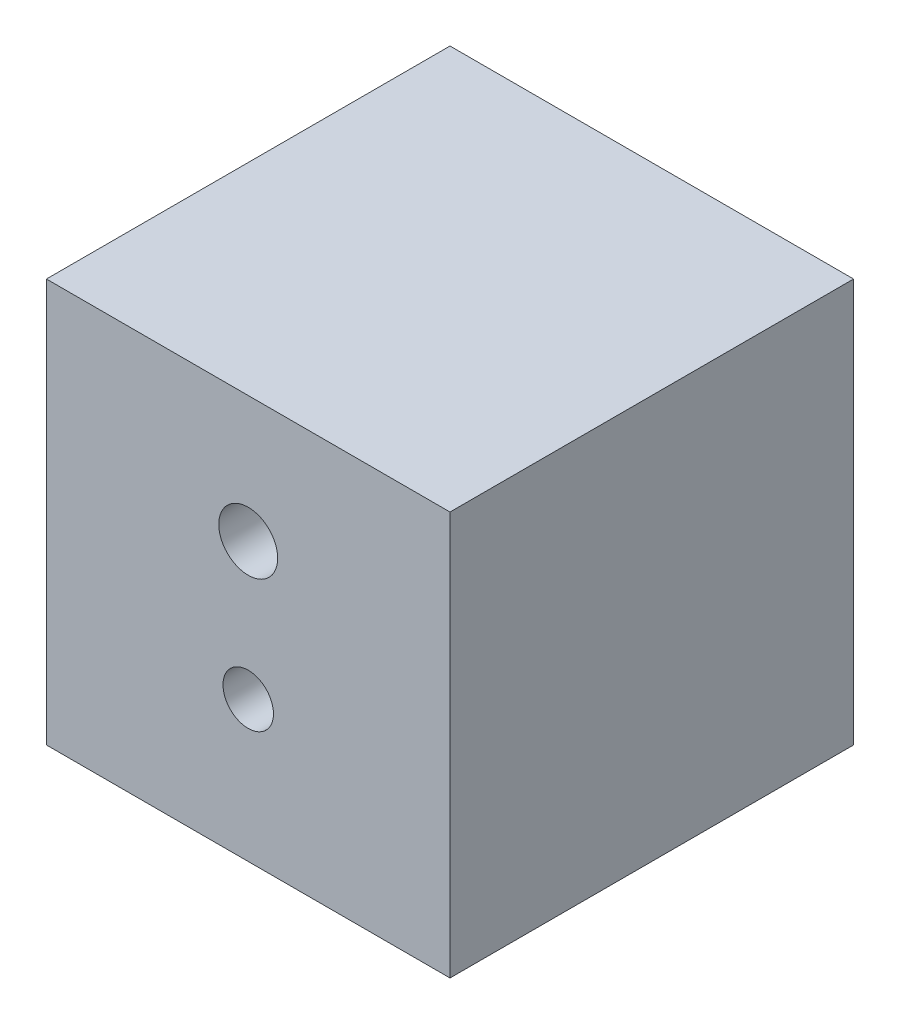
SolidWorks part; units mm, degrees
ref_plane "Front Plane" through (0, 0, 0) normal (0, 0, 1) x (1, 0, 0)
ref_plane "Top Plane" through (0, 0, 0) normal (0, 1, 0) x (1, 0, 0)
ref_plane "Right Plane" through (0, 0, 0) normal (1, 0, 0) x (0, 0, -1)
sketch "Sketch2" plane through (0, 0, 0) normal (0, 1, 0) x (1, 0, 0)
  line L1 (-38.1, -38.1) -> (38.1, -38.1)
  line L2 (-38.1, -38.1) -> (-38.1, 38.1)
  line L3 (-38.1, 38.1) -> (38.1, 38.1)
  line L4 (38.1, -38.1) -> (38.1, 38.1)
  line L5 (-38.1, -38.1) -> (38.1, 38.1) construction
  line L6 (-38.1, 38.1) -> (38.1, -38.1) construction
  point P0 (0, 0)
  dimension "D1" = 76.2
  dimension "D2" = 76.2
extrude "Boss-Extrude1" add sketch "Sketch2" along normal blind 76.2
sketch "Sketch3" plane through (0, 0, 38.1) normal (0, 0, 1) x (1, 0, 0)
  line L2 (0, 52.367) -> (0, 26.5225) construction
  line L3 (-38.1, 0) -> (38.1, 0) construction
  circle A0 centre (0, 26.5225) radius 4.7625
  circle A1 centre (0, 52.367) radius 5.5626
  point P4 (0, 39.4448)
  point P7 (0, 0)
  dimension "D1" = 9.525
  dimension "D3" = 25.8445
  dimension "D4" = 11.1252
extrude "Cut-Extrude1" cut sketch "Sketch3" against normal blind 72.39
sketch "Sketch4" plane through (0, 0, 38.1) normal (0, 0, 1) x (1, 0, 0)
  line L0 (0, 52.367) -> (0, 26.5225) construction
  circle A0 centre (0, 27.7925) radius 2.4023
  dimension "D1" = 24.5745
sketch "Sketch5" plane through (0, 0, -34.29) normal (0, 0, 1) x (1, 0, 0)
  circle A0 centre (0, 52.367) radius 5.5626
extrude "Boss-Extrude2" add sketch "Sketch5" along normal offset from surface (62.23 mm away) 10.16 up to face at (4.7625, 26.5225, 38.1)
equation "\"D1@Sketch2\"=\"D2@Sketch2\""
equation "\"D1@Boss-Extrude1\"=\"D2@Sketch2\""
